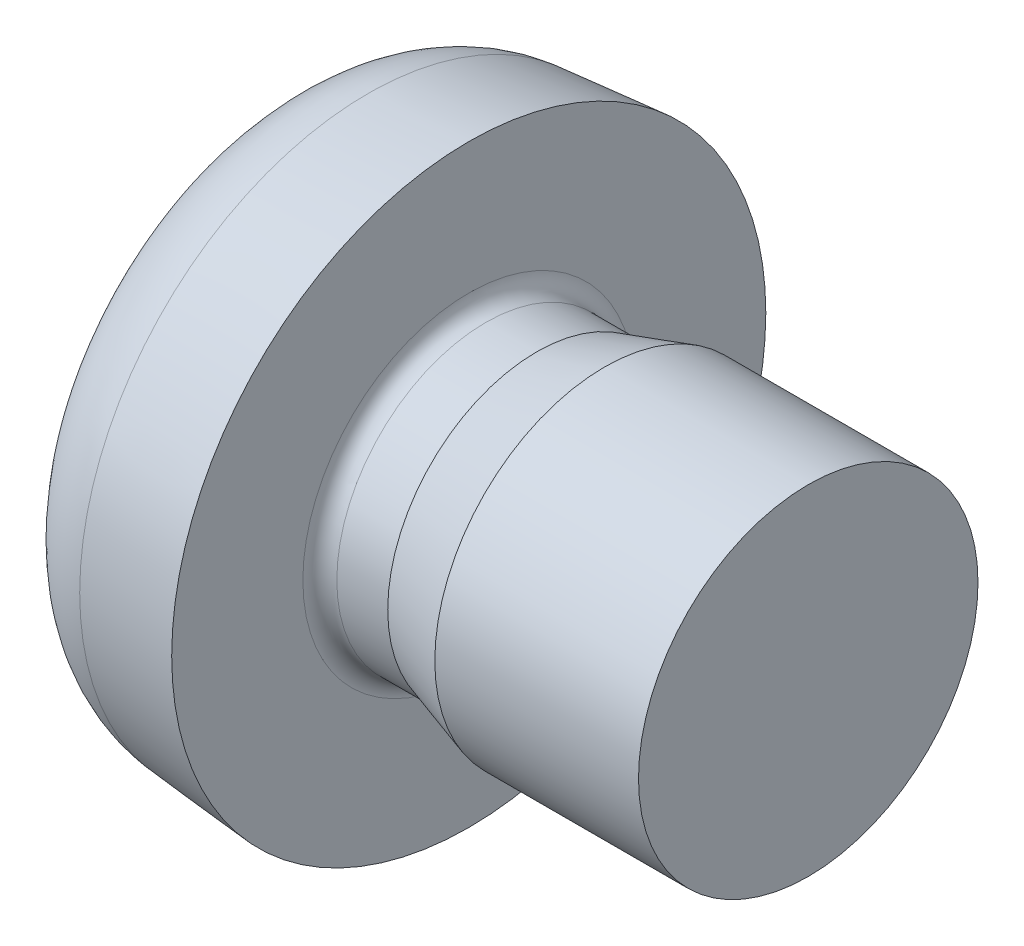
SolidWorks part; units mm, degrees
material "2014 合金"
ref_plane "正面" through (0, 0, 0) normal (0, 0, 1) x (1, 0, 0)
ref_plane "平面" through (0, 0, 0) normal (0, 1, 0) x (1, 0, 0)
ref_plane "右側面" through (0, 0, 0) normal (1, 0, 0) x (0, 0, -1)
ref_plane "平面1" through (0, 0, 0) normal (0, 0, 1) x (1, 0, 0)
sketch "ｽｹｯﾁ1" plane through (0, 0, 0) normal (0, 0, 1) x (1, 0, 0)
  line L0 (-0.5939, 1.698) -> (0, 1.75)
  line L1 (0, 1.75) -> (0, 0.9773)
  line L2 (0.1, 0.8773) -> (0.4, 0.8773)
  line L3 (0.4, 0.8773) -> (0.8, 1)
  line L4 (0.8, 1) -> (2, 1)
  line L5 (2, 1) -> (2, 0)
  line L6 (2, 0) -> (-1.3, 0)
  line L7 (2, 0) -> (-1.3, 0) construction
  arc A0 (-1.3, 0) -> (-1.1172, 1.2696) centre (3.2, 0) cw
  arc A1 (-1.1172, 1.2696) -> (-0.5939, 1.698) centre (-0.5416, 1.1003) cw
  arc A2 (0, 0.9773) -> (0.1, 0.8773) centre (0.1, 0.9773) ccw
revolve "回転1" add sketch "ｽｹｯﾁ1" angle 360 about L7
cosmetic thread "ねじ山1" parameters "D1"=1.2, "D2"=1.509
ref_plane "平面2" through (-1.3, 0, 0) normal (1, 0, 0) x (0, 0, -1)
sketch "ｽｹｯﾁ2" plane through (-1.3, 0, 0) normal (1, 0, 0) x (0, 0, -1)
  line L0 (-1.1, 0.2333) -> (-1.1, -0.2333)
  line L1 (-1.1, -0.2333) -> (-0.5833, -0.2333)
  line L2 (-0.2333, -0.5833) -> (-0.2333, -1.1)
  line L3 (-0.2333, -1.1) -> (0.2333, -1.1)
  line L4 (0.2333, -1.1) -> (0.2333, -0.5833)
  line L5 (0.5833, -0.2333) -> (1.1, -0.2333)
  line L6 (1.1, -0.2333) -> (1.1, 0.2333)
  line L7 (1.1, 0.2333) -> (0.5833, 0.2333)
  line L8 (0.2333, 0.5833) -> (0.2333, 1.1)
  line L9 (0.2333, 1.1) -> (-0.2333, 1.1)
  line L10 (-0.2333, 1.1) -> (-0.2333, 0.5833)
  line L11 (-0.5833, 0.2333) -> (-1.1, 0.2333)
  arc A0 (-0.5833, -0.2333) -> (-0.2333, -0.5833) centre (-0.5833, -0.5833) cw
  arc A1 (0.2333, -0.5833) -> (0.5833, -0.2333) centre (0.5833, -0.5833) cw
  arc A2 (0.5833, 0.2333) -> (0.2333, 0.5833) centre (0.5833, 0.5833) cw
  arc A3 (-0.2333, 0.5833) -> (-0.5833, 0.2333) centre (-0.5833, 0.5833) cw
extrude "ｶｯﾄ - 押し出し1" cut sketch "ｽｹｯﾁ2" along normal blind 0.65
